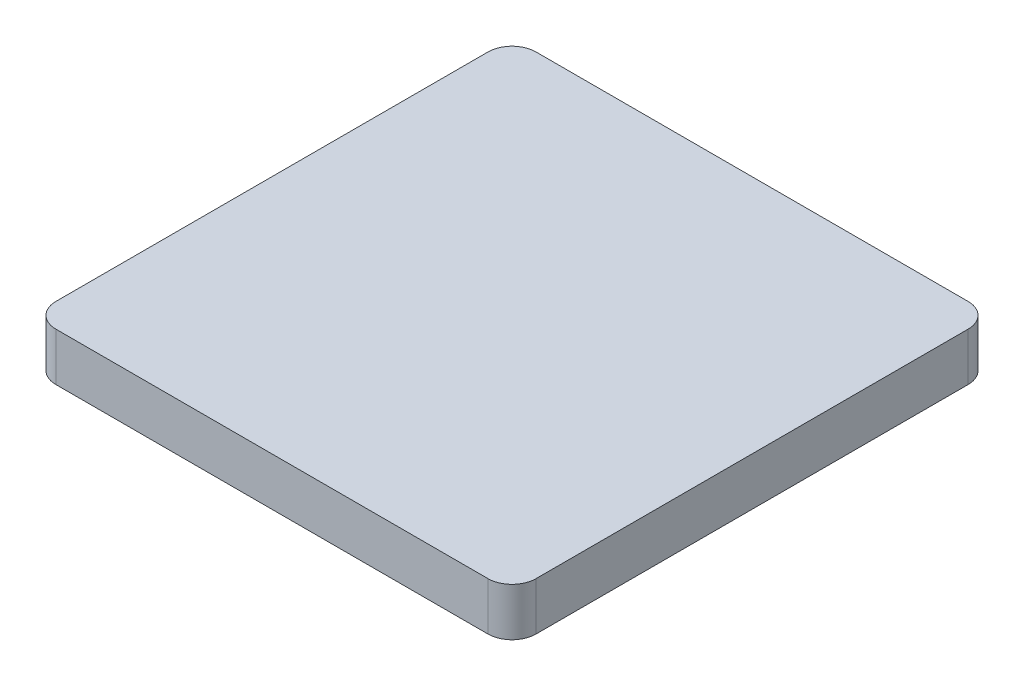
SolidWorks part; units mm, degrees
ref_plane "Front Plane" through (0, 0, 0) normal (0, 0, 1) x (1, 0, 0)
ref_plane "Top Plane" through (0, 0, 0) normal (0, 1, 0) x (1, 0, 0)
ref_plane "Right Plane" through (0, 0, 0) normal (1, 0, 0) x (0, 0, -1)
sketch "Sketch1" plane through (0, 0, 0) normal (0, 1, 0) x (1, 0, 0)
  line L1 (0, 0) -> (60, 0)
  line L2 (0, 0) -> (0, 60)
  line L3 (0, 60) -> (60, 60)
  line L4 (60, 0) -> (60, 60)
  dimension "D1" = 60
sketch "Sketch2" plane through (0, 0, 0) normal (0, 1, 0) x (1, 0, 0)
  line L0 (0, 0) -> (60, 0)
  line L1 (0, 0) -> (0, 60)
  line L2 (0, 60) -> (60, 60)
  line L3 (60, 0) -> (60, 60)
extrude "Boss-Extrude1" add sketch "Sketch2" along normal blind 6
fillet "Fillet1" radius 3 4 edges at (0, 3, -60) (60, 3, -60) (0, 3, 0) (60, 3, 0)
